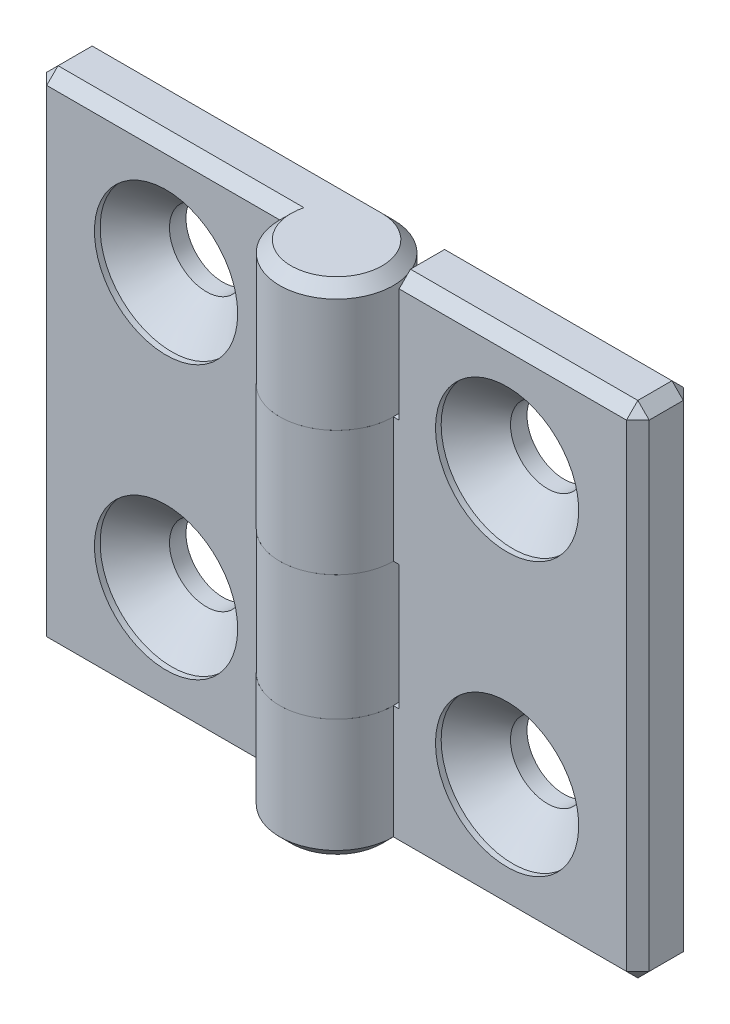
SolidWorks part; units mm, degrees
material "Нейлон"
ref_plane "Спереди" through (0, 0, 0) normal (0, 0, 1) x (1, 0, 0)
ref_plane "Сверху" through (0, 0, 0) normal (0, 1, 0) x (1, 0, 0)
ref_plane "Справа" through (0, 0, 0) normal (1, 0, 0) x (0, 0, -1)
sketch "Эскиз1" plane through (0, 0, 0) normal (0, 1, 0) x (1, 0, 0)
  line L0 (0, 5) -> (-26.5, 5)
  line L1 (-26.5, 5) -> (-26.5, 0)
  line L3 (-26.5, 0) -> (-5, 0)
  line L4 (0, 0) -> (0, 10.5526) construction
  arc A0 (-5, 0) -> (0, 5) centre (0, 0) ccw
  dimension "D1" = 53
  dimension "D2" = 5
extrude "Бобышка-Вытянуть1" add sketch "Эскиз1" along normal mid plane 44
sketch "Эскиз3" plane through (0, 0, 0) normal (0, 0, 1) x (1, 0, 0)
  line L0 (5, -22) -> (5, 22) construction
  line L1 (-5.5, 11) -> (5, 11)
  line L2 (-5.5, 11) -> (-5.5, 0)
  line L3 (-5.5, 0) -> (5, 0)
  line L4 (5, 11) -> (5, 0)
  line L5 (5, 0) -> (5, -11) construction
  line L6 (5, -22) -> (-5.5, -22)
  line L7 (5, -22) -> (5, -11)
  line L8 (5, -11) -> (-5.5, -11)
  line L9 (-5.5, -22) -> (-5.5, -11)
  line L10 (5, 11) -> (5, 22) construction
  line L11 (-5, 22) -> (-5, -22) construction
  dimension "D1" = 0.5
extrude "Вырез-Вытянуть1" cut sketch "Эскиз3" against normal through all and the other way through all
hole_wizard "Зенковка для винта с полупотайной головкой M61" positions "Эскиз4" profile "Эскиз6" countersink size "M6" standard "ISO" end condition through all
sketch "Эскиз4" plane through (0, 0, 0) normal (0, 0, 1) x (1, 0, 0)
  line L0 (-15, 12) -> (-15, -12)
  line L2 (0, 0) -> (0, 18.9001) construction
  line L3 (5, 0) -> (-5, 0) construction
  point P0 (-15, 12)
  point P2 (-15, -12)
  point P9 (-15, 0)
  dimension "D1" = 24
  dimension "D2" = 30
sketch "Эскиз6" plane through (-15, 12, 0) normal (1, 0, 0) x (0, -1, 0)
  line L0 (0, 0) -> (0, 5)
  line L1 (0, 5) -> (3.25, 5)
  line L2 (3.25, 5) -> (3.25, 3.55)
  line L3 (3.25, 3.55) -> (6.3, 0.5)
  line L4 (6.3, 0.5) -> (6.3, 0)
  line L6 (6.3, 0) -> (0, 0)
  line L7 (-3.25, 3.55) -> (-6.3, 0.5) construction
  line L11 (0, -6.35) -> (0, 107.95) construction
  dimension "Диаметр сквозного отверстия" = 6.5
  dimension "Глубина сквозного отверстия" = 5
  dimension "Диаметр зенковки" = 12.6
  dimension "Угол зенковки" = 90
  dimension "Утопленность" = 0.5
chamfer "Фаска1" distance 1 angle 45 9 edges at (-16, -22, 0) (-26.5, 0, 0) (-15.75, 22, 0) (-26.5, -22, -2.5) (-26.5, 22, -2.5) (3.5355, 22, 3.5355) (-13.25, 22, -5) (-26.5, 0, -5) (-16, -22, -5)
sketch "Угол раскрытия" plane through (0, 0, 0) normal (0, 1, 0) x (1, 0, 0)
  line L0 (0, 0) -> (0, -10)
  line L7 (0, 5) -> (-26.5, 5) construction
  dimension "D1" = 10
  dimension "D2" = 90
pattern_circular "Круговой массив1" count 2 over 360 about axis through (0, 0, 0) along (0, 0, 1) of bodies 106
